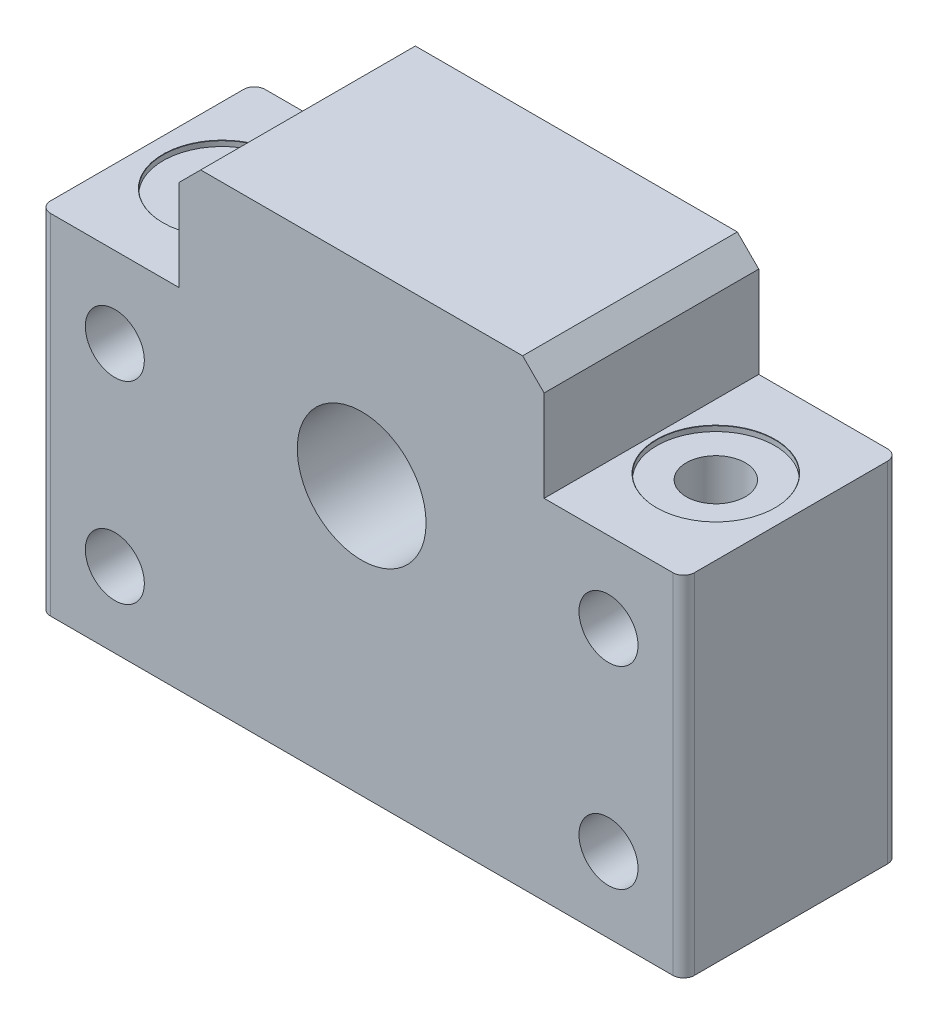
SolidWorks part; units mm, degrees
material "6061 合金"
ref_plane "前视基准面" through (0, 0, 0) normal (0, 0, 1) x (1, 0, 0)
ref_plane "上视基准面" through (0, 0, 0) normal (0, 1, 0) x (1, 0, 0)
ref_plane "右视基准面" through (0, 0, 0) normal (1, 0, 0) x (0, 0, -1)
sketch "草图1" plane through (0, 0, 0) normal (0, 0, 1) x (1, 0, 0)
  line L0 (0, 29.0816) -> (0, -23.5714) construction
  line L1 (-17, 16.25) -> (-17, 26.75)
  line L2 (-30, 16.25) -> (-17, 16.25)
  line L3 (-30, 16.25) -> (-30, -16.25)
  line L4 (-30, -16.25) -> (30, -16.25)
  line L5 (30, 16.25) -> (30, -16.25)
  line L6 (-30, 16.25) -> (30, -16.25) construction
  line L7 (-30, -16.25) -> (30, 16.25) construction
  line L8 (-17, 26.75) -> (17, 26.75)
  line L9 (17, 26.75) -> (17, 16.25)
  line L10 (-23, 16.25) -> (-23, -16.25) construction
  line L11 (17, 16.25) -> (30, 16.25)
  circle A0 centre (0, 8.75) radius 6
  circle A1 centre (-23, 8.75) radius 2.75
  circle A2 centre (-23, -9.25) radius 2.75
  circle A3 centre (23, -9.25) radius 2.75
  circle A4 centre (23, 8.75) radius 2.75
  point P3 (0, 0)
  dimension "D3" = 12
  dimension "D4" = 25
  dimension "D7" = 5.5
  dimension "D8" = 18
  dimension "D9" = 46
  dimension "D1" = 60
  dimension "D2" = 32.5
  dimension "D5" = 34
  dimension "D6" = 43
extrude "凸台-拉伸1" add sketch "草图1" along normal blind 20
chamfer "倒角1" distance 2 angle 45 2 edges at (-17, 26.75, 10) (17, 26.75, 10)
sketch "草图2" plane through (0, 16.25, 0) normal (0, 1, 0) x (1, 0, 0)
  line L0 (-30, -10) -> (30, -10) construction
  line L1 (-30, -20) -> (-30, 0) construction
  line L2 (30, -20) -> (30, 0) construction
  line L3 (0, 0) -> (0, -20) construction
  line L4 (15, -20) -> (-15, -20) construction
  circle A0 centre (-23, -10) radius 3.3
  circle A1 centre (23, -10) radius 3.3
  dimension "D1" = 46
  dimension "D2" = 6.6
fillet "圆角1" radius 1 4 edges at (-30, 0, 0) (-30, 0, 20) (30, 0, 0) (30, 0, 20)
hole_wizard "M5 六角头螺栓的柱形沉头孔1" positions "3D草图1" profile "草图3" counterbore size "M5" standard "GB" end condition through all
sketch3d "3D草图1"
  point P4 (23, 16.25, 10)
  point P9 (-23, 16.25, 10)
sketch "草图3" plane through (23, 16.25, 10) normal (1, 0, 0) x (0, 0, 1)
  line L0 (0, 0) -> (0, 32.5)
  line L1 (0, 32.5) -> (2.75, 32.5)
  line L3 (2.75, 32.5) -> (2.75, 0.5)
  line L4 (5.5, 0.5) -> (2.75, 0.5)
  line L5 (5.5, 0.5) -> (5.5, 0.025)
  line L6 (5.5, 0.025) -> (5.525, 0)
  line L7 (5.525, 0) -> (0, 0)
  line L8 (-5.5, 0.025) -> (-5.525, 0) construction
  line L11 (0, -6.35) -> (0, 107.95) construction
  dimension "通孔孔直径" = 5.5
  dimension "通孔孔深度" = 32.5
  dimension "柱形沉头孔直径" = 11
  dimension "柱形沉头孔深度" = 0.5
  dimension "近端锥形沉头孔直径" = 11.05
  dimension "近端锥形沉头孔角度" = 90
